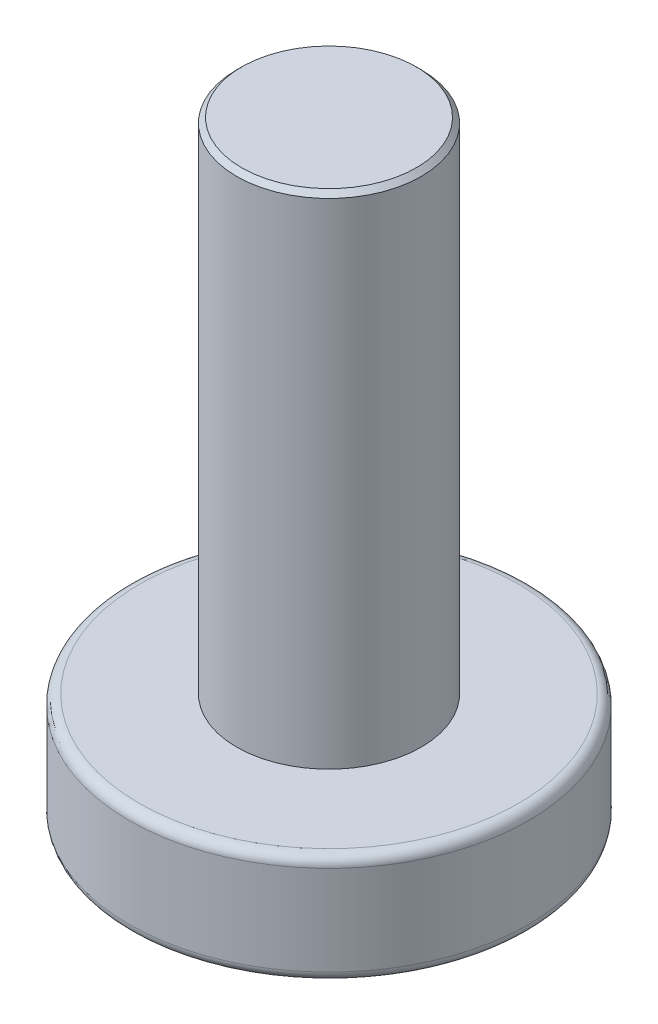
SolidWorks part; units mm, degrees
ref_plane "Спереди" through (0, 0, 0) normal (0, 0, 1) x (1, 0, 0)
ref_plane "Сверху" through (0, 0, 0) normal (0, 1, 0) x (1, 0, 0)
ref_plane "Справа" through (0, 0, 0) normal (1, 0, 0) x (0, 0, -1)
sketch "Эскиз1" plane through (0, 0, 0) normal (0, 1, 0) x (1, 0, 0)
  circle A0 centre (0, 0) radius 4
  dimension "D1" = 8
extrude "Бобышка-Вытянуть1" add sketch "Эскиз1" along normal blind 2.2
sketch "Эскиз2" plane through (0, 2.2, 0) normal (0, 1, 0) x (1, 0, 0)
  circle A0 centre (0, 0) radius 1.85
  dimension "D1" = 3.7
extrude "Бобышка-Вытянуть2" add sketch "Эскиз2" along normal blind 10
chamfer "Фаска1" distance 0.1 angle 45 1 edges at (0, 12.2, 1.85)
fillet "Скругление1" radius 0.2 2 edges at (0, 2.2, 4) (0, 0, 4)
sketch "Эскиз3" plane through (0, 0, 0) normal (0, -1, 0) x (1, 0, 0)
  line L0 (-0.5, 0.5) -> (-0.5, 2)
  line L1 (-0.5, 2) -> (0.5, 2)
  line L2 (0.5, 2) -> (0.5, 0.5)
  line L3 (0.5, 0.5) -> (2, 0.5)
  line L4 (2, 0.5) -> (2, -0.5)
  line L5 (2, -0.5) -> (0.5, -0.5)
  line L6 (0.5, -0.5) -> (0.5, -2)
  line L7 (0.5, -2) -> (-0.5, -2)
  line L8 (-0.5, -2) -> (-0.5, -0.5)
  line L9 (-0.5, -0.5) -> (-2, -0.5)
  line L10 (-2, -0.5) -> (-2, 0.5)
  line L11 (-2, 0.5) -> (-0.5, 0.5)
  point P12 (0, 2)
  point P13 (0, -2)
  point P15 (-2, 0)
  point P16 (2, 0)
  dimension "D1" = 4
  dimension "D2" = 1
extrude "Вырез-Вытянуть1" cut sketch "Эскиз3" against normal blind 1.5
